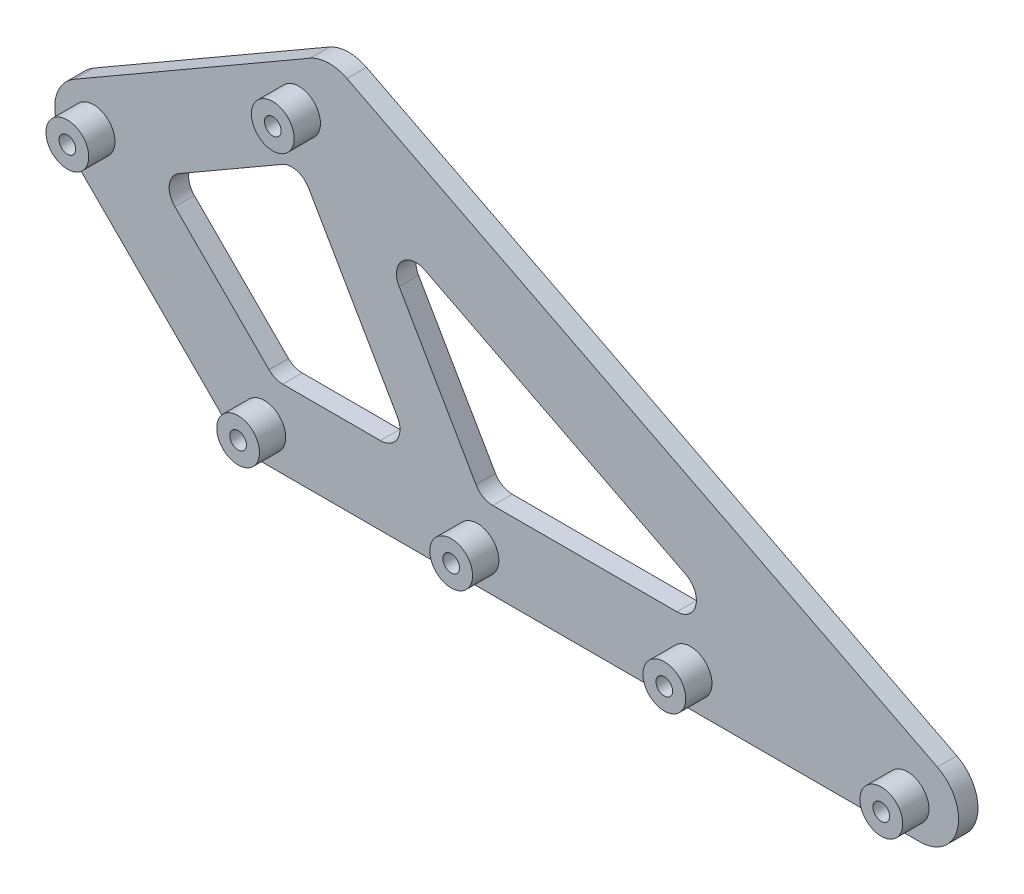
SolidWorks part; units mm, degrees
ref_plane "Front" through (0, 0, 0) normal (0, 0, 1) x (1, 0, 0)
ref_plane "Top" through (0, 0, 0) normal (0, 1, 0) x (1, 0, 0)
ref_plane "Right" through (0, 0, 0) normal (1, 0, 0) x (0, 0, -1)
sketch "Sketch1" plane through (0, 0, 0) normal (0, 0, 1) x (1, 0, 0)
  line L0 (0, 0) -> (170, 0) construction
  line L1 (0, 10) -> (170, 10)
  line L2 (0, -10) -> (170, -10)
  line L3 (0, 0) -> (-42.4264, 42.4264) construction
  line L4 (-7.0711, -7.0711) -> (-49.4975, 35.3553)
  line L5 (7.0711, 7.0711) -> (-35.3553, 49.4975)
  line L6 (-42.4264, 42.4264) -> (18.1954, 77.4264) construction
  line L7 (-47.4264, 51.0867) -> (13.1954, 86.0867)
  line L8 (-37.4264, 33.7662) -> (23.1954, 68.7662)
  line L9 (18.1954, 77.4264) -> (170, 0) construction
  line L10 (22.7389, 86.3346) -> (174.5435, 8.9082)
  line L11 (13.6518, 68.5182) -> (165.4565, -8.9082)
  arc A0 (0, 10) -> (0, -10) centre (0, 0) ccw
  arc A1 (170, -10) -> (170, 10) centre (170, 0) ccw
  arc A2 (-7.0711, -7.0711) -> (7.0711, 7.0711) centre (0, 0) ccw
  arc A3 (-35.3553, 49.4975) -> (-49.4975, 35.3553) centre (-42.4264, 42.4264) ccw
  arc A4 (-47.4264, 51.0867) -> (-37.4264, 33.7662) centre (-42.4264, 42.4264) ccw
  arc A5 (23.1954, 68.7662) -> (13.1954, 86.0867) centre (18.1954, 77.4264) ccw
  arc A6 (22.7389, 86.3346) -> (13.6518, 68.5182) centre (18.1954, 77.4264) ccw
  arc A7 (165.4565, -8.9082) -> (174.5435, 8.9082) centre (170, 0) ccw
  point P3 (85, 0)
  point P10 (-21.2132, 21.2132)
  point P17 (-12.1155, 59.9264)
  point P24 (94.0977, 38.7132)
  dimension "D2" = 10
  dimension "D1" = 170
  dimension "D3" = 60
  dimension "D4" = 45
  dimension "D5" = 70
  dimension "D6" = 30
extrude "Boss-Extrude1" add sketch "Sketch1" along normal blind 5 contours A6 L7 A3 L5 L8 L11 | A5 L8 L11 L1 A1 L10 | A7 L11 L1 L5 A2 L2 | A4 L4 A0 L1 L5 L8 | L11 A7 A1 L1 | A5 A6 L11 L8 | A3 A4 L8 L5 | A0 A2 L5 L1
sketch "Sketch2" plane through (0, 0, 5) normal (0, 0, 1) x (1, 0, 0)
  line L0 (-26.1401, 40.2823) -> (18.4909, 66.0501) construction
  line L1 (4.1421, 10) -> (-26.1401, 40.2823) construction
  line L2 (4.1421, 10) -> (128.3844, 10) construction
  line L3 (18.4909, 66.0501) -> (128.3844, 10) construction
  line L4 (-26.1401, 40.2823) -> (18.4909, 66.0501)
  line L5 (4.1421, 10) -> (-26.1401, 40.2823)
  line L6 (4.1421, 10) -> (128.3844, 10)
  line L7 (18.4909, 66.0501) -> (128.3844, 10)
  line L8 (10.3668, 61.3596) -> (40.0192, 10)
  line L9 (27.6873, 61.3596) -> (57.3397, 10)
  line M15 (18.4909, 66.0501) -> (128.3844, 10)
  dimension "D1" = 60
  dimension "D2" = 15
extrude "Boss-Extrude2" add sketch "Sketch2" against normal through all contours L9 L4 L8 L6 M15
fillet "Fillet1" radius 5 7 edges at (128.3844, 10, 2.5) (27.6873, 61.3596, 2.5) (57.3397, 10, 2.5) (40.0192, 10, 2.5) (4.1421, 10, 2.5) (-26.1401, 40.2823, 2.5) (10.3668, 61.3596, 2.5)
sketch "Sketch3" plane through (0, 0, 5) normal (0, 0, 1) x (1, 0, 0)
  line L0 (-42.4264, 42.4264) -> (1.4849, -1.4849) construction
  line L1 (-7.0711, -7.0711) -> (-49.4975, 35.3553) construction
  line L2 (-7.0711, -7.0711) -> (-49.4975, 35.3553)
  line L3 (1.4849, -1.4849) -> (56.2849, -1.4849) construction
  line L4 (56.2849, -1.4849) -> (111.0849, -1.4849) construction
  line L5 (0, -10) -> (170, -10) construction
  line L6 (0, -10) -> (170, -10)
  line L7 (111.0849, -1.4849) -> (166.8849, -1.4849) construction
  line L8 (-42.4264, 42.4264) -> (10.4011, 72.9264) construction
  line L9 (-47.4264, 51.0867) -> (13.1954, 86.0867) construction
  line L10 (-47.4264, 51.0867) -> (13.1954, 86.0867)
  arc A0 (-47.4264, 51.0867) -> (-49.4975, 35.3553) centre (-42.4264, 42.4264) ccw construction
  arc A1 (-47.4264, 51.0867) -> (-49.4975, 35.3553) centre (-42.4264, 42.4264) ccw
  circle A2 centre (-42.4264, 42.4264) radius 2.15
  circle A3 centre (-42.4264, 42.4264) radius 5.5
  circle A4 centre (1.4849, -1.4849) radius 5.5
  circle A5 centre (1.4849, -1.4849) radius 2.15
  circle A6 centre (56.2849, -1.4849) radius 2.15
  circle A7 centre (56.2849, -1.4849) radius 5.5
  circle A8 centre (111.0849, -1.4849) radius 2.15
  circle A9 centre (111.0849, -1.4849) radius 5.5
  circle A10 centre (166.8849, -1.4849) radius 2.15
  circle A11 centre (166.8849, -1.4849) radius 5.5
  circle A12 centre (10.4011, 72.9264) radius 5.5
  circle A13 centre (10.4011, 72.9264) radius 2.15
  dimension "D1" = 11
  dimension "D2" = 4.3
  dimension "D3" = 62.1
  dimension "D4" = 54.8
  dimension "D5" = 54.8
  dimension "D6" = 55.8
  dimension "D7" = 61
extrude "Boss-Extrude3" add sketch "Sketch3" along normal blind 6.75 contours A3 A2 | A4 | A7 | A9 | A11 | A5 | A6 | A8 | A10 | A12 | A13
sketch "Sketch4" plane through (0, 0, 5) normal (0, 0, 1) x (1, 0, 0)
  circle A0 centre (-42.4264, 42.4264) radius 2.15 construction
  circle A1 centre (-42.4264, 42.4264) radius 2.15
  circle A2 centre (1.4849, -1.4849) radius 2.15 construction
  circle A3 centre (1.4849, -1.4849) radius 2.15
  circle A4 centre (56.2849, -1.4849) radius 2.15 construction
  circle A5 centre (56.2849, -1.4849) radius 2.15
  circle A6 centre (111.0849, -1.4849) radius 2.15 construction
  circle A7 centre (111.0849, -1.4849) radius 2.15
  circle A8 centre (166.8849, -1.4849) radius 2.15 construction
  circle A9 centre (166.8849, -1.4849) radius 2.15
  circle A10 centre (10.4011, 72.9264) radius 2.15 construction
  circle A11 centre (10.4011, 72.9264) radius 2.15
extrude "Cut-Extrude1" cut sketch "Sketch4" against normal through all
